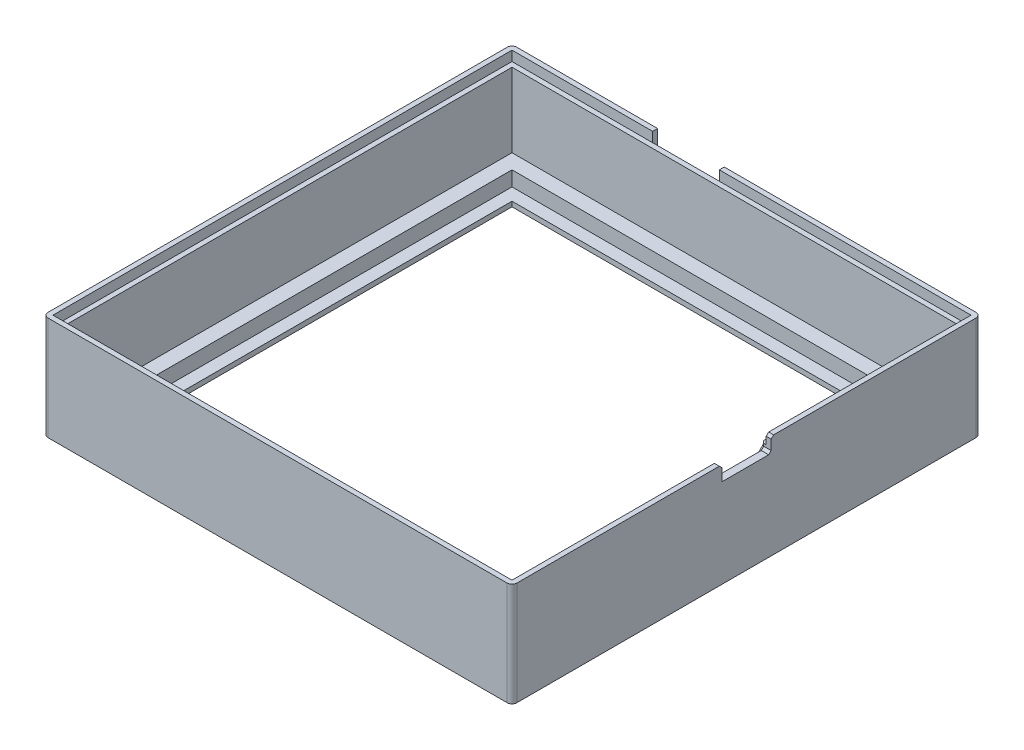
SolidWorks part; units mm, degrees
ref_plane "Front Plane" through (0, 0, 0) normal (0, 0, 1) x (1, 0, 0)
ref_plane "Top Plane" through (0, 0, 0) normal (0, 1, 0) x (1, 0, 0)
ref_plane "Right Plane" through (0, 0, 0) normal (1, 0, 0) x (0, 0, -1)
sketch "Sketch1" plane through (0, 0, 0) normal (0, 1, 0) x (1, 0, 0)
  line L1 (-46.5, -47.5) -> (46.5, -47.5)
  line L2 (-47.5, -46.5) -> (-47.5, 46.5)
  line L3 (-46.5, 47.5) -> (46.5, 47.5)
  line L4 (47.5, -46.5) -> (47.5, 46.5)
  line L5 (-47.5, -47.5) -> (47.5, 47.5) construction
  line L6 (-47.5, 47.5) -> (47.5, -47.5) construction
  arc A0 (46.5, -47.5) -> (47.5, -46.5) centre (46.5, -46.5) ccw
  arc A1 (-47.5, 46.5) -> (-46.5, 47.5) centre (-46.5, 46.5) cw
  arc A2 (-46.5, -47.5) -> (-47.5, -46.5) centre (-46.5, -46.5) cw
  arc A3 (46.5, 47.5) -> (47.5, 46.5) centre (46.5, 46.5) cw
  point P0 (0, 0)
  dimension "D3" = 1
  dimension "D4" = 1
  dimension "D1" = 95
  dimension "D2" = 95
extrude "Boss-Extrude1" add sketch "Sketch1" along normal blind 4
sketch "Sketch2" plane through (0, 4, 0) normal (0, 1, 0) x (1, 0, 0)
  line L1 (-40, -40) -> (40, -40)
  line L2 (-40, -40) -> (-40, 40)
  line L3 (-40, 40) -> (40, 40)
  line L4 (40, -40) -> (40, 40)
  line L5 (-40, -40) -> (40, 40) construction
  line L6 (-40, 40) -> (40, -40) construction
  point P0 (0, 0)
  dimension "D1" = 80
  dimension "D2" = 80
sketch "Sketch4" plane through (0, 4, 0) normal (0, 1, 0) x (1, 0, 0)
  line L8 (45.5, -45.5) -> (45.5, 45.5)
  line L9 (45.5, 45.5) -> (-45.5, 45.5)
  line L10 (-45.5, 45.5) -> (-45.5, -45.5)
  line L11 (-45.5, -45.5) -> (45.5, -45.5)
  line L12 (45.5, -45.5) -> (45.5, 45.5)
  line L13 (45.5, 45.5) -> (-45.5, 45.5)
  line L14 (-45.5, 45.5) -> (-45.5, -45.5)
  line L15 (-45.5, -45.5) -> (45.5, -45.5)
  line L16 (47.5, -46.5) -> (47.5, 46.5)
  line L17 (46.5, 47.5) -> (-46.5, 47.5)
  line L18 (-47.5, 46.5) -> (-47.5, -46.5)
  line L19 (-46.5, -47.5) -> (46.5, -47.5)
  line L20 (47.5, -46.5) -> (47.5, 46.5)
  line L21 (46.5, 47.5) -> (-46.5, 47.5)
  line L22 (-47.5, 46.5) -> (-47.5, -46.5)
  line L23 (-46.5, -47.5) -> (46.5, -47.5)
  arc A16 (46.5, -47.5) -> (47.5, -46.5) centre (46.5, -46.5) ccw
  arc A17 (47.5, 46.5) -> (46.5, 47.5) centre (46.5, 46.5) ccw
  arc A18 (-46.5, 47.5) -> (-47.5, 46.5) centre (-46.5, 46.5) ccw
  arc A19 (-47.5, -46.5) -> (-46.5, -47.5) centre (-46.5, -46.5) ccw
  arc A20 (46.5, -47.5) -> (47.5, -46.5) centre (46.5, -46.5) ccw
  arc A21 (47.5, 46.5) -> (46.5, 47.5) centre (46.5, 46.5) ccw
  arc A22 (-46.5, 47.5) -> (-47.5, 46.5) centre (-46.5, 46.5) ccw
  arc A23 (-47.5, -46.5) -> (-46.5, -47.5) centre (-46.5, -46.5) ccw
  dimension "D1" = 2
  dimension "D2" = 0
extrude "Boss-Extrude2" add sketch "Sketch4" along normal blind 15
extrude "Cut-Extrude3" cut sketch "Sketch2" against normal up to next
sketch "Sketch7" plane through (47.5, 0, 0) normal (1, 0, 0) x (0, 0, -1)
  line L0 (-46.5, 19) -> (46.5, 19) construction
  line L1 (-5, 18) -> (5, 18)
  line L2 (-5, 18) -> (-5, 19)
  line L3 (-5, 19) -> (5, 19)
  line L4 (5, 18) -> (5, 19)
  line L5 (-5, 18) -> (5, 19) construction
  line L6 (-5, 19) -> (5, 18) construction
  point P0 (0, 18.5)
  dimension "D1" = 1
  dimension "D2" = 10
extrude "Cut-Extrude6" cut sketch "Sketch7" against normal up to next
sketch "Sketch8" plane through (0, 4, 0) normal (0, 1, 0) x (1, 0, 0)
  line L1 (-42.5, -42.5) -> (42.5, -42.5)
  line L2 (-42.5, -42.5) -> (-42.5, 42.5)
  line L3 (-42.5, 42.5) -> (42.5, 42.5)
  line L4 (42.5, -42.5) -> (42.5, 42.5)
  line L5 (-42.5, -42.5) -> (42.5, 42.5) construction
  line L6 (-42.5, 42.5) -> (42.5, -42.5) construction
  point P0 (0, 0)
  dimension "D1" = 85
  dimension "D2" = 85
extrude "Cut-Extrude7" cut sketch "Sketch8" against normal blind 3
sketch "Sketch10" plane through (0, 19, 0) normal (0, 1, 0) x (1, 0, 0)
  line L0 (46.5, 5) -> (46.5, 46.5)
  line L1 (46.5, 46.5) -> (-46.5, 46.5)
  line L2 (-46.5, 46.5) -> (-46.5, -46.5)
  line L3 (-46.5, -46.5) -> (46.5, -46.5)
  line L4 (46.5, -46.5) -> (46.5, -5)
  line L5 (46.5, -5) -> (47.5, -5)
  line L6 (46.5, 5) -> (47.5, 5)
  line L12 (45.5, 45.5) -> (45.5, 5)
  line L14 (47.5, 5) -> (47.5, 46.5)
  line L15 (46.5, 47.5) -> (-46.5, 47.5)
  line L16 (-47.5, 46.5) -> (-47.5, -46.5)
  line L17 (-46.5, -47.5) -> (46.5, -47.5)
  line L18 (47.5, -46.5) -> (47.5, -5)
  line L20 (45.5, -5) -> (45.5, -45.5)
  line L21 (45.5, -45.5) -> (-45.5, -45.5)
  line L22 (-45.5, -45.5) -> (-45.5, 45.5)
  line L23 (-45.5, 45.5) -> (45.5, 45.5)
  line L26 (47.5, 5) -> (47.5, 46.5)
  line L27 (46.5, 47.5) -> (-46.5, 47.5)
  line L28 (-47.5, 46.5) -> (-47.5, -46.5)
  line L29 (-46.5, -47.5) -> (46.5, -47.5)
  line L30 (47.5, -46.5) -> (47.5, -5)
  line L38 (45.5, 5) -> (47.5, 5)
  line L40 (47.5, -5) -> (45.5, -5)
  arc A0 (46.5, 46.5) -> (46.5, 46.5) centre (46.5, 46.5) ccw
  arc A1 (-46.5, 46.5) -> (-46.5, 46.5) centre (-46.5, 46.5) ccw
  arc A2 (-46.5, -46.5) -> (-46.5, -46.5) centre (-46.5, -46.5) ccw
  arc A3 (46.5, -46.5) -> (46.5, -46.5) centre (46.5, -46.5) ccw
  arc A4 (47.5, 46.5) -> (46.5, 47.5) centre (46.5, 46.5) ccw
  arc A5 (-46.5, 47.5) -> (-47.5, 46.5) centre (-46.5, 46.5) ccw
  arc A6 (-47.5, -46.5) -> (-46.5, -47.5) centre (-46.5, -46.5) ccw
  arc A7 (46.5, -47.5) -> (47.5, -46.5) centre (46.5, -46.5) ccw
  arc A8 (47.5, 46.5) -> (46.5, 47.5) centre (46.5, 46.5) ccw
  arc A9 (-46.5, 47.5) -> (-47.5, 46.5) centre (-46.5, 46.5) ccw
  arc A10 (-47.5, -46.5) -> (-46.5, -47.5) centre (-46.5, -46.5) ccw
  arc A11 (46.5, -47.5) -> (47.5, -46.5) centre (46.5, -46.5) ccw
  dimension "D1" = 0
  dimension "D2" = 1
extrude "Boss-Extrude3" add sketch "Sketch10" along normal blind 2
chamfer "Chamfer1" distance 0.5 angle 45 6 edges at (47, 21, 5) (46, 19, 5) (47, 21, -5) (45.5, 18, 0) (45.5, 18.5, -5) (46.5, 18, -5)
sketch "Sketch11" plane through (0, 0, -47.5) normal (0, 0, -1) x (-1, 0, 0)
  line L0 (-46.5, 21) -> (46.5, 21) construction
  line L1 (16, 20) -> (6.5, 20)
  line L2 (16, 20) -> (16, 21)
  line L3 (16, 21) -> (6.5, 21)
  line L4 (6.5, 20) -> (6.5, 21)
  line L5 (47.5, 21) -> (47.5, 0) construction
  dimension "D1" = 1
  dimension "D2" = 9.5
  dimension "D3" = 31.5
extrude "Cut-Extrude8" cut sketch "Sketch11" against normal up to next
sketch "Sketch12" plane through (0, 0, -47.5) normal (0, 0, -1) x (-1, 0, 0)
  line L0 (16, 20) -> (16, 21) construction
  line L1 (6.5, 20) -> (16, 20) construction
  line L2 (6.5, 21) -> (6.5, 20) construction
  line L3 (16, 20) -> (16, 21)
  line L4 (6.5, 20) -> (16, 20)
  line L5 (6.5, 21) -> (6.5, 20)
  line L6 (4.5, 21) -> (4.5, 18)
  line L7 (4.5, 18) -> (18, 18)
  line L8 (18, 18) -> (18, 21)
  line L9 (4.5, 21) -> (6.5, 21)
  line L10 (16, 21) -> (18, 21)
  dimension "D1" = 2
extrude "Cut-Extrude10" cut sketch "Sketch12" against normal blind 1
